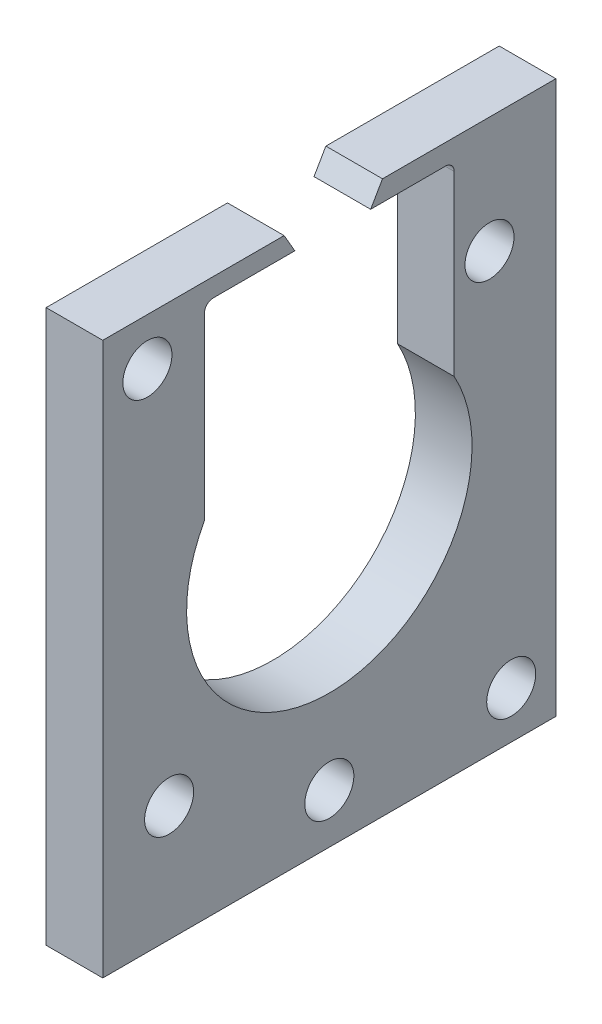
SolidWorks part; units mm, degrees
ref_plane "Front Plane" through (0, 0, 0) normal (0, 0, 1) x (1, 0, 0)
ref_plane "Top Plane" through (0, 0, 0) normal (0, 1, 0) x (1, 0, 0)
ref_plane "Right Plane" through (0, 0, 0) normal (1, 0, 0) x (0, 0, -1)
sketch "Sketch1" plane through (0, 0, 0) normal (1, 0, 0) x (0, 0, -1)
  line L45 (0, 0) -> (50.8, 0)
  line L46 (0, 0) -> (0, 61.92)
  line L47 (0, 61.92) -> (50.8, 61.92)
  line L48 (50.8, 0) -> (50.8, 61.92)
  dimension "D1" = 61.92
  dimension "D2" = 50.8
extrude "Boss-Extrude2" add sketch "Sketch1" along normal blind 6.35
sketch "Sketch2" plane through (0, 0, 0) normal (-1, 0, 0) x (0, 0, 1)
  circle A13 centre (-25.4, 30.9607) radius 16
extrude "Cut-Extrude1" cut sketch "Sketch2" against normal through all
sketch "Sketch4" plane through (6.35, 0, 0) normal (1, 0, 0) x (0, 0, -1)
  line L1 (11.4, 59.8393) -> (11.4, 37.92)
  line L2 (11.4, 37.92) -> (39.4, 37.92)
  line L3 (39.4, 37.92) -> (39.4, 59.62)
  line L8 (11.4, 59.8393) -> (21.5347, 59.8393)
  line L9 (21.5347, 59.8393) -> (18.306, 65.4315)
  line L12 (25.4, 0) -> (25.4, 61.92) construction
  line L13 (0, 0) -> (50.8, 0) construction
  line L14 (50.8, 61.92) -> (0, 61.92) construction
  line L16 (30.0347, 59.62) -> (33.39, 65.4315)
  line L17 (18.306, 65.4315) -> (33.39, 65.4315)
  line L18 (39.4, 59.62) -> (30.0347, 59.62)
  point P0 (11.5226, 60.0841)
  point P28 (25.4, 37.92)
  dimension "D3" = 2.3
  dimension "D5" = 60
  dimension "D6" = 8.5
  dimension "D10" = 28
  dimension "D4" = 60
  dimension "D2" = 24
extrude "Cut-Extrude4" cut sketch "Sketch4" against normal through all
sketch "Sketch5" plane through (0, 0, 0) normal (-1, 0, 0) x (0, 0, 1)
  circle A0 centre (-45.7955, 5.2725) radius 2.75 construction
  circle A1 centre (-25.3997, 5.5607) radius 2.75 construction
  circle A2 centre (-7.4395, 13.0002) radius 2.75 construction
  circle A3 centre (-45.7955, 5.2725) radius 2.75
  circle A4 centre (-25.3997, 5.5607) radius 2.75
  circle A5 centre (-7.4395, 13.0002) radius 2.75
  circle A6 centre (-43.3599, 48.9208) radius 2.75 construction
  circle A7 centre (-5.0045, 56.6481) radius 2.75 construction
  circle A8 centre (-43.3599, 48.9208) radius 2.75
  circle A9 centre (-5.0045, 56.6481) radius 2.75
extrude "Cut-Extrude5" cut sketch "Sketch5" against normal up to next
fillet "Fillet1" radius 1 2 edges at (3.175, 59.62, -39.4) (3.175, 59.8393, -11.4)
